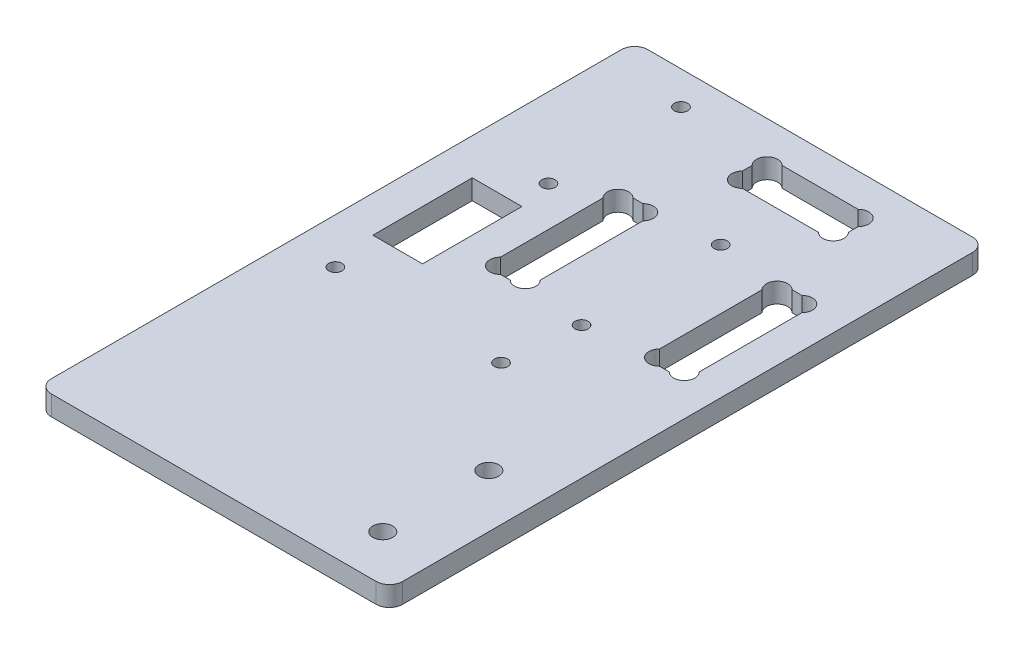
SolidWorks part; units mm, degrees
ref_plane "Plan de face" through (0, 0, 0) normal (0, 0, 1) x (1, 0, 0)
ref_plane "Plan de dessus" through (0, 0, 0) normal (0, 1, 0) x (1, 0, 0)
ref_plane "Plan de droite" through (0, 0, 0) normal (1, 0, 0) x (0, 0, -1)
sketch "Esquisse1" plane through (0, 0, 0) normal (0, 1, 0) x (1, 0, 0)
  line L6 (0, 88) -> (0, 2)
  line L7 (2, 0) -> (51, 0)
  line L8 (53, 88) -> (53, 2)
  line L11 (2, 90) -> (51, 90)
  arc A0 (51, 90) -> (53, 88) centre (51, 88) cw
  arc A1 (2, 90) -> (0, 88) centre (2, 88) ccw
  arc A2 (51, 0) -> (53, 2) centre (51, 2) ccw
  arc A3 (0, 2) -> (2, 0) centre (2, 2) ccw
  point P3 (26.5, 0)
  dimension "D3" = 2
  dimension "D5" = 2
  dimension "D4" = 2
  dimension "D1" = 53
  dimension "D2" = 90
extrude "Extrusion1" add sketch "Esquisse1" along normal blind 3
sketch "Esquisse2" plane through (0, 0, 0) normal (0, -1, 0) x (1, 0, 0)
  line L0 (53, -2) -> (53, -88) construction
  line L1 (51, -90) -> (2, -90) construction
  line L2 (2, 0) -> (51, 0) construction
  line L4 (53, -2) -> (53, -88) construction
  line L16 (41, -82.7373) -> (41, -81.2627)
  line L18 (45.7373, -49.5) -> (44.2627, -49.5)
  line L19 (45.7373, -69.5) -> (44.2627, -69.5)
  line L20 (25, -82.7373) -> (25, -81.2627)
  line L21 (38.7373, -85) -> (27.2627, -85)
  line L22 (38.7373, -79) -> (27.2627, -79)
  line L23 (48, -67.2373) -> (48, -51.7627)
  line L24 (42, -67.2373) -> (42, -51.7627)
  line L25 (24, -67.2373) -> (24, -51.7627)
  line L26 (18, -67.2373) -> (18, -51.7627)
  line L27 (20.2627, -69.5) -> (21.7373, -69.5)
  line L28 (20.2627, -49.5) -> (21.7373, -49.5)
  arc A0 (44.2627, -49.5) -> (42, -51.7627) centre (43.1314, -50.6314) ccw
  arc A1 (38.7373, -85) -> (41, -82.7373) centre (39.8686, -83.8686) ccw
  arc A2 (38.7373, -79) -> (41, -81.2627) centre (39.8686, -80.1314) cw
  arc A3 (27.2627, -85) -> (25, -82.7373) centre (26.1314, -83.8686) cw
  arc A4 (27.2627, -79) -> (25, -81.2627) centre (26.1314, -80.1314) ccw
  arc A5 (45.7373, -49.5) -> (48, -51.7627) centre (46.8686, -50.6314) cw
  arc A6 (44.2627, -69.5) -> (42, -67.2373) centre (43.1314, -68.3686) cw
  arc A7 (45.7373, -69.5) -> (48, -67.2373) centre (46.8686, -68.3686) ccw
  arc A8 (20.2627, -69.5) -> (18, -67.2373) centre (19.1314, -68.3686) cw
  arc A9 (21.7373, -69.5) -> (24, -67.2373) centre (22.8686, -68.3686) ccw
  arc A10 (20.2627, -49.5) -> (18, -51.7627) centre (19.1314, -50.6314) ccw
  arc A11 (21.7373, -49.5) -> (24, -51.7627) centre (22.8686, -50.6314) cw
  circle A12 centre (45, -23) radius 1.5
  circle A13 centre (45, -7) radius 1.5
  dimension "D15" = 2.2627
  dimension "D17" = 1.1314
  dimension "D11" = 1.6
  dimension "D32" = 3
  dimension "D33" = 3
  dimension "D1" = 6
  dimension "D2" = 6
  dimension "D3" = 6
  dimension "D4" = 18
  dimension "D5" = 20
  dimension "D6" = 16
  dimension "D7" = 5
  dimension "D8" = 1
  dimension "D9" = 9.5
  dimension "D10" = 5
  dimension "D12" = 1.1314
  dimension "D13" = 1.1314
  dimension "D14" = 2.2627
  dimension "D16" = 1.1314
  dimension "D18" = 1.1314
  dimension "D19" = 1.1314
  dimension "D20" = 2.2627
  dimension "D21" = 2.2627
  dimension "D22" = 1.1314
  dimension "D23" = 1.1314
  dimension "D24" = 1.1314
  dimension "D25" = 1.1314
  dimension "D26" = 1.1314
  dimension "D27" = 1.1314
  dimension "D28" = 2.2627
  dimension "D29" = 2.2627
  dimension "D30" = 2.2627
  dimension "D31" = 2.2627
  dimension "D34" = 16
  dimension "D35" = 7
  dimension "D36" = 8
extrude "Enlèv. mat.-Extru.1" cut sketch "Esquisse2" against normal through all
sketch "Esquisse4" plane through (0, 3, 0) normal (0, 1, 0) x (1, 0, 0)
  line L0 (51, 90) -> (2, 90) construction
  line L1 (0, 88) -> (0, 2) construction
  line L2 (53, 2) -> (53, 88) construction
  line L3 (5.5, 60) -> (13, 60)
  line L4 (5.5, 60) -> (5.5, 45)
  line L5 (5.5, 45) -> (13, 45)
  line L6 (13, 60) -> (13, 45)
  circle A0 centre (12, 85) radius 1
  circle A1 centre (12, 65) radius 1
  circle A2 centre (33, 70) radius 1
  circle A3 centre (33, 49) radius 1
  dimension "D1" = 2
  dimension "D2" = 5
  dimension "D4" = 12
  dimension "D14" = 2
  dimension "D3" = 20
  dimension "D5" = 15
  dimension "D6" = 7.5
  dimension "D7" = 5
  dimension "D8" = 1
  dimension "D10" = 20
  dimension "D12" = 20
  dimension "D13" = 21
extrude "Enlèv. mat.-Extru.2" cut sketch "Esquisse4" against normal through all
sketch "Esquisse5" plane through (0, 3, 0) normal (0, 1, 0) x (1, 0, 0)
  line L0 (0, 88) -> (0, 2) construction
  line L2 (5.5, 45) -> (13, 45) construction
  circle A0 centre (6.8474, 38) radius 1
  circle A1 centre (31.8474, 38) radius 1
  point P8 (0, 0)
  dimension "D4" = 2
  dimension "D1" = 6.8474
  dimension "D2" = 25
  dimension "D3" = 7
extrude "Enlèv. mat.-Extru.3" cut sketch "Esquisse5" against normal through all
